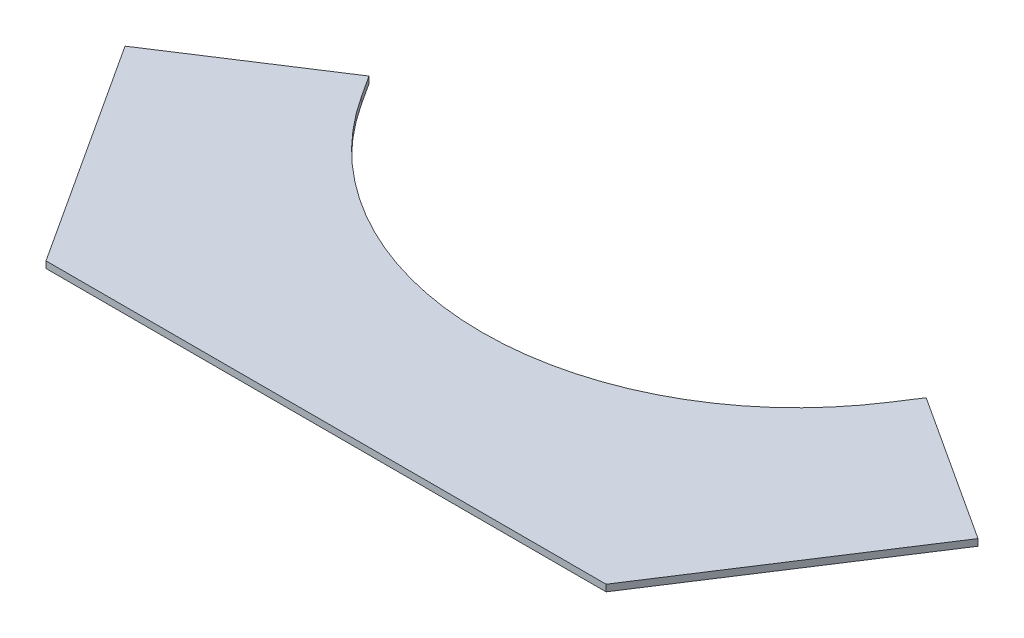
SolidWorks part; units mm, degrees
ref_plane "Front Plane" through (0, 0, 0) normal (0, 0, 1) x (1, 0, 0)
ref_plane "Top Plane" through (0, 0, 0) normal (0, 1, 0) x (1, 0, 0)
ref_plane "Right Plane" through (0, 0, 0) normal (1, 0, 0) x (0, 0, -1)
sketch "Sketch1" plane through (0, 0, 0) normal (0, 1, 0) x (1, 0, 0)
  line L0 (0, 0) -> (534.9068, 0)
  line L1 (674.7582, 215.3522) -> (534.9068, 0)
  line L2 (-139.8514, 215.3522) -> (0, 0)
  line L3 (674.7582, 215.3522) -> (533.5061, 307.0824)
  line L4 (-139.8514, 215.3522) -> (1.4007, 307.0824)
  line L7 (1.4007, 307.0824) -> (15.0167, 286.1156)
  line L10 (533.5061, 307.0824) -> (519.8901, 286.1156)
  arc A0 (15.0167, 286.1156) -> (519.8901, 286.1156) centre (267.4534, 450.05) ccw
extrude "Boss-Extrude1" add sketch "Sketch1" along normal blind 6.35
